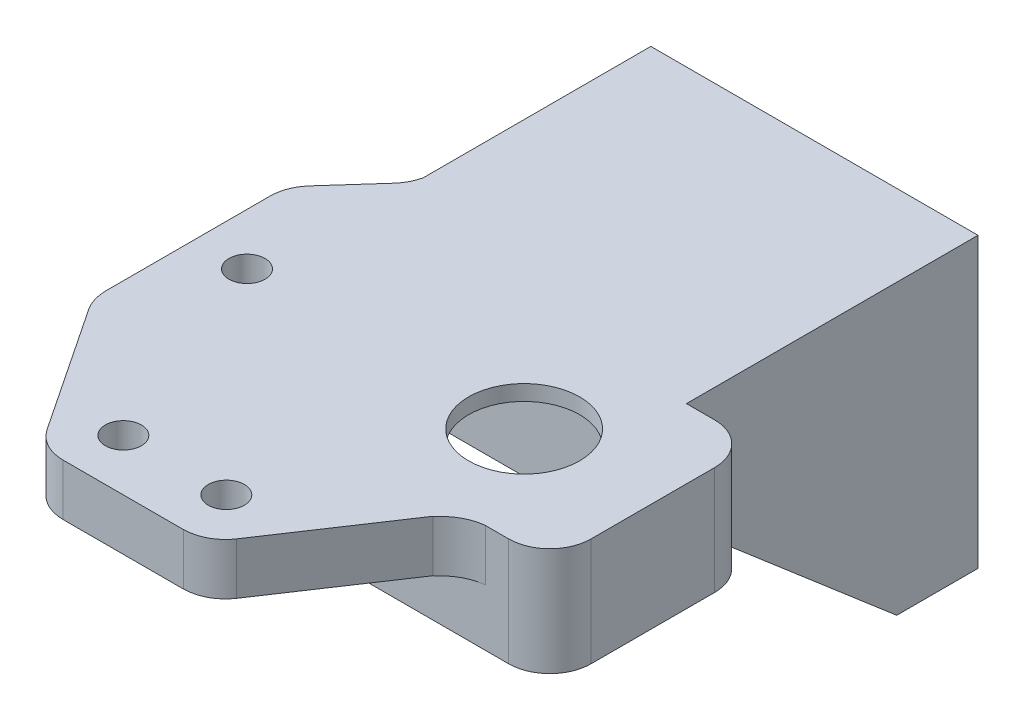
SolidWorks part; units mm, degrees
ref_plane "Alzado" through (0, 0, 0) normal (0, 0, 1) x (1, 0, 0)
ref_plane "Planta" through (0, 0, 0) normal (0, 1, 0) x (1, 0, 0)
ref_plane "Vista lateral" through (0, 0, 0) normal (1, 0, 0) x (0, 0, -1)
sketch "Croquis2" plane through (0, 0, 0) normal (0, 1, 0) x (1, 0, 0)
  line L0 (-15.9202, -3.4567) -> (19.0798, -3.4567)
  line L1 (19.0798, -3.4567) -> (19.0798, 16.5433)
  line L2 (19.0798, 16.5433) -> (-15.9202, 16.5433)
  line L3 (-15.9202, 16.5433) -> (-15.9202, -3.4567)
  dimension "D1" = 35
  dimension "D2" = 20
extrude "Saliente-Extruir1" add sketch "Croquis2" along normal blind 10.5
sketch "Croquis3" plane through (0, 0, 0) normal (0, -1, 0) x (1, 0, 0)
  line L0 (-9.9202, -0.0433) -> (-9.9202, -13.0433)
  line L1 (-9.9202, -13.0433) -> (13.0798, -13.0433)
  line L2 (13.0798, -13.0433) -> (13.0798, -0.0433)
  line L3 (13.0798, -0.0433) -> (-9.9202, -0.0433)
  line L4 (-15.9202, 3.4567) -> (19.0798, 3.4567) construction
  line L5 (19.0798, 3.4567) -> (19.0798, -16.5433) construction
  dimension "D1" = 23
  dimension "D2" = 13
  dimension "D3" = 3.5
  dimension "D4" = 6
extrude "Cortar-Extruir1" cut sketch "Croquis3" against normal blind 9
sketch "Croquis4" plane through (0, 0, 0) normal (0, -1, 0) x (1, 0, 0)
  line L0 (-9.9202, -0.0433) -> (-9.9202, -13.0433) construction
  line L1 (-15.9202, 3.4567) -> (19.0798, 3.4567) construction
  line L2 (13.0798, -13.0433) -> (13.0798, -0.0433) construction
  circle A0 centre (-12.2202, -6.5433) radius 1
  circle A1 centre (15.3798, -6.5433) radius 1
  dimension "D1" = 2
  dimension "D4" = 2.3
  dimension "D2" = 2.3
  dimension "D3" = 10
  dimension "D5" = 10
extrude "Cortar-Extruir2" cut sketch "Croquis4" against normal blind 4
sketch "Croquis5" plane through (0, 9, 0) normal (0, -1, 0) x (1, 0, 0)
  line L0 (13.0798, -0.0433) -> (-9.9202, -0.0433) construction
  line L1 (-9.9202, -0.0433) -> (-9.9202, -13.0433) construction
  circle A0 centre (6.5798, -6.5433) radius 5.386
  dimension "D1" = 10.772
  dimension "D2" = 6.5
  dimension "D3" = 16.5
extrude "Cortar-Extruir3" cut sketch "Croquis5" against normal blind 4
fillet "Redondeo1" radius 4 4 edges at (19.0798, 5.25, 3.4567) (-15.9202, 5.25, 3.4567) (-15.9202, 5.25, -16.5433) (19.0798, 5.25, -16.5433)
sketch "Croquis9" plane through (0, 10.5, 0) normal (0, 1, 0) x (1, 0, 0)
  line L0 (15.0798, 16.5433) -> (12.3366, 16.5433)
  line L1 (15.0798, 16.5433) -> (-11.9202, 16.5433) construction
  line L2 (1.8526, 25.3713) -> (9.5086, 17.7143)
  line L3 (-0.9754, 26.5433) -> (-19.3184, 26.5433)
  line L4 (-19.3184, 26.5433) -> (-19.3184, 23.5993)
  line L5 (13.0798, 0.0433) -> (-9.9202, 0.0433) construction
  line L6 (-20.3382, 20.9333) -> (-24.3012, 16.5023)
  line L7 (-25.3202, 13.8353) -> (-25.3202, -2.2447)
  line L8 (-24.6492, -4.4627) -> (-16.5092, -16.6747)
  line L9 (-13.1822, -18.4567) -> (-1.4642, -18.4567)
  line L10 (9.4928, -5.2377) -> (1.8628, -16.6747)
  line L11 (12.8208, -3.4567) -> (15.0798, -3.4567)
  line L12 (19.0798, 12.5433) -> (19.0798, 0.5433)
  arc A0 (19.0798, 12.5433) -> (15.0798, 16.5433) centre (15.0798, 12.5433) ccw construction
  arc A1 (15.0798, -3.4567) -> (19.0798, 0.5433) centre (15.0798, 0.5433) ccw construction
  spline S0 degree 2 poles (12.3366, 16.5433) (10.6986, 16.5878) (9.5086, 17.7143) knots 0 0 0 1 1 1
  spline S1 degree 2 poles (1.8526, 25.3713) (0.6624, 26.4974) (-0.9754, 26.5433) knots 0 0 0 1 1 1
  spline S2 degree 2 poles (-19.3184, 23.5993) (-19.3581, 22.0864) (-20.3382, 20.9333) knots 0 0 0 1 1 1
  spline S3 degree 2 poles (-24.3012, 16.5023) (-25.2821, 15.3489) (-25.3202, 13.8353) knots 0 0 0 1 1 1
  spline S4 degree 2 poles (-25.3202, -2.2447) (-25.2872, -3.4567) (-24.6492, -4.4627) knots 0 0 0 1 1 1
  spline S5 degree 2 poles (-16.5092, -16.6747) (-15.2925, -18.3998) (-13.1822, -18.4567) knots 0 0 0 1 1 1
  spline S6 degree 2 poles (-1.4642, -18.4567) (0.6651, -18.358) (1.8628, -16.6747) knots 0 0 0 1 1 1
  spline S7 degree 2 poles (9.4928, -5.2377) (10.9831, -3.6364) (12.8208, -3.4567) knots 0 0 0 0.396538 0.396538 0.396538
  spline S8 degree 2 poles (15.0798, -3.4567) (18.7366, -3.1135) (19.0798, 0.5433) knots 0 0 0 1 1 1
  spline S9 degree 2 poles (15.0798, 16.5433) (18.7366, 16.2002) (19.0798, 12.5433) knots 0 0 0 1 1 1
  point P5 (10.8106, 16.8583)
  point P6 (9.5086, 17.7143)
  point P9 (1.8526, 25.3713)
  point P12 (0.5506, 26.2273)
  point P13 (-0.9754, 26.5433)
  point P15 (-19.5932, 22.1763)
  point P19 (-20.3382, 20.9333)
  point P22 (-24.3012, 16.5023)
  point P25 (-25.0462, 15.2593)
  point P26 (-25.3202, 13.8353)
  point P30 (-25.0432, -3.6777)
  point P31 (-24.6492, -4.4627)
  point P33 (-16.5092, -16.6747)
  point P38 (-15.0692, -17.9827)
  point P40 (-13.1822, -18.4567)
  point P42 (0.6978, -17.8057)
  point P45 (1.8628, -16.6747)
  point P47 (9.4928, -5.2377)
  point P50 (12.8208, -3.4567)
  point P58 (17.9082, 15.3717)
  point P59 (17.9082, -2.2851)
  dimension "D1" = 2.7431
  dimension "D2" = 1.526
  dimension "D3" = 3.815
  dimension "D4" = 1.302
  dimension "D5" = 4.671
  dimension "D6" = 7.656
  dimension "D7" = 12.328
  dimension "D8" = 1.302
  dimension "D9" = 13.184
  dimension "D10" = 1.526
  dimension "D11" = 13.5
  dimension "D12" = 18.343
  dimension "D13" = 2.944
  dimension "D14" = 4.367
  dimension "D15" = 9.673
  dimension "D16" = 5.61
  dimension "D17" = 10.418
  dimension "D18" = 10.041
  dimension "D19" = 14.381
  dimension "D20" = 11.284
  dimension "D21" = 15.126
  dimension "D22" = 15.4
  dimension "D23" = 12.708
  dimension "D24" = 16.08
  dimension "D25" = 0.277
  dimension "D26" = 0.394
  dimension "D27" = 1.433
  dimension "D28" = 0.785
  dimension "D29" = 8.14
  dimension "D30" = 16.718
  dimension "D31" = 1.44
  dimension "D32" = 18.026
  dimension "D33" = 1.887
  dimension "D34" = 18.5
  dimension "D35" = 11.718
  dimension "D36" = 2.162
  dimension "D37" = 17.849
  dimension "D38" = 1.165
  dimension "D39" = 16.718
  dimension "D40" = 5.281
  dimension "D41" = 3.587
  dimension "D42" = 3.328
  dimension "D43" = 3.5
  dimension "D44" = 2.259
extrude "Saliente-Extruir2" add sketch "Croquis9" against normal blind 5
sketch "Croquis13" plane through (0, 0, 0) normal (0, -1, 0) x (1, 0, 0)
  line L0 (-9.9202, -0.0433) -> (-9.9202, -13.0433)
  line L1 (-9.9202, -13.0433) -> (13.0798, -13.0433)
  line L2 (13.0798, -13.0433) -> (13.0798, -0.0433)
  line L3 (13.0798, -0.0433) -> (-9.9202, -0.0433)
extrude "Cortar-Extruir4" cut sketch "Croquis13" against normal blind 9
sketch "Croquis14" plane through (0, 9, 0) normal (0, -1, 0) x (1, 0, 0)
  line L0 (13.0798, -0.0433) -> (-9.9202, -0.0433) construction
  line L1 (-9.9202, -0.0433) -> (-9.9202, -13.0433) construction
  circle A0 centre (6.5798, -6.5433) radius 5.386
  dimension "D3" = 10.772
  dimension "D1" = 6.5
  dimension "D2" = 16.5
extrude "Cortar-Extruir5" cut sketch "Croquis14" against normal up to next
sketch "Croquis15" plane through (0, 10.5, 0) normal (0, 1, 0) x (1, 0, 0)
  line L0 (-9.9202, 0.0433) -> (-9.9202, 13.0433) construction
  line L1 (13.0798, 0.0433) -> (-9.9202, 0.0433) construction
  line L2 (-24.6492, -4.4627) -> (-16.5092, -16.6747) construction
  line L3 (1.8628, -16.6747) -> (9.4928, -5.2377) construction
  circle A0 centre (-20.3202, 6.5443) radius 1.75
  circle A1 centre (-12.3243, -13.4532) radius 1.75
  circle A2 centre (-2.3243, -13.4567) radius 1.75
  dimension "D1" = 3.5
  dimension "D4" = 3.5
  dimension "D2" = 10.4
  dimension "D3" = 7.291
  dimension "D5" = 10
  dimension "D6" = 13.5
  dimension "D7" = 5.269
  dimension "D8" = 5.269
extrude "Cortar-Extruir6" cut sketch "Croquis15" against normal up to next
sketch "Croquis16" plane through (0, 10.5, 0) normal (0, 1, 0) x (1, 0, 0)
  line L0 (-19.3184, 26.5433) -> (-19.3184, 44.8418)
  line L1 (-19.3184, 44.8418) -> (12.3366, 44.8418)
  line L2 (12.3366, 16.5433) -> (12.3366, 44.8418)
  line L3 (-19.3184, 26.5433) -> (-0.9754, 26.5433)
  line L4 (1.8526, 25.3713) -> (9.5086, 17.7143)
  parabola Q0 (12.3366, 16.5433) -> (9.5086, 17.7143) focus (11.5758, 18.7062) apex (10.8106, 16.8583) construction
  parabola Q1 (1.8526, 25.3713) -> (-0.9754, 26.5433) focus (-0.2166, 24.3763) apex (0.5506, 26.2273) construction
  spline S0 degree 2 poles (9.5086, 17.7143) (10.6986, 16.5878) (12.3366, 16.5433) knots 0 0 0 1 1 1
  spline S1 degree 2 poles (-0.9754, 26.5433) (0.6624, 26.4974) (1.8526, 25.3713) knots 0 0 0 1 1 1
sketch "Croquis17" plane through (19.0798, 0, 0) normal (1, 0, 0) x (0, 0, -1)
  line L0 (44.8418, 10.5) -> (44.8418, -17.5)
  line L1 (16.5433, 10.5) -> (44.8418, 10.5) construction
  line L2 (44.8418, -17.5) -> (16.5433, -17.5)
  line L3 (16.5433, -17.5) -> (16.5433, 10.5)
  line L4 (16.5433, 10.5) -> (44.8418, 10.5)
  dimension "D1" = 28
extrude "Saliente-Extruir5" add sketch "Croquis17" against normal blind 38.5
sketch "Croquis18" plane through (0, 10.5, 0) normal (0, 1, 0) x (1, 0, 0)
  line L0 (12.3366, 16.5433) -> (19.0798, 16.5433)
  line L1 (19.0798, 16.5433) -> (19.0798, 44.8418)
  line L2 (19.0798, 44.8418) -> (12.3366, 44.8418)
  line L3 (12.3366, 44.8418) -> (12.3366, 16.5433)
extrude "Cortar-Extruir7" cut sketch "Croquis18" against normal blind 38.5
sketch "Croquis19" plane through (0, 0, -16.5433) normal (0, 0, 1) x (1, 0, 0)
  line L0 (-16.4202, -17.5) -> (9.3366, -17.5)
  line L1 (-19.4202, -17.5) -> (12.3366, -17.5) construction
  line L2 (9.3366, -17.5) -> (9.3366, 2.5)
  line L3 (9.3366, 2.5) -> (-16.4202, 2.5)
  line L4 (-16.4202, 2.5) -> (-16.4202, -17.5)
  line L5 (-19.4202, 5.5) -> (-19.4202, -17.5) construction
  line L6 (12.3366, -17.5) -> (12.3366, 0) construction
  line L7 (-19.4202, 5.5) -> (-11.9202, 5.5) construction
  dimension "D1" = 3
  dimension "D2" = 3
  dimension "D3" = 3
extrude "Cortar-Extruir8" cut sketch "Croquis19" against normal blind 20.5
sketch "Croquis20" plane through (0, 0, -37.0433) normal (0, 0, 1) x (1, 0, 0)
  line L0 (-16.4202, -17.5) -> (9.3366, -17.5) construction
  line L1 (-13.1822, 5.5) -> (-1.4642, 5.5) construction
  line L2 (-19.4202, 5.5) -> (-19.4202, -17.5) construction
  line L3 (-7.0418, -2.5) -> (-0.0418, -2.5)
  line L5 (-0.0418, -9.5) -> (-7.0418, -9.5)
  arc A0 (-7.0418, -2.5) -> (-7.0418, -9.5) centre (-7.0418, -6) ccw
  arc A1 (-0.0418, -2.5) -> (-0.0418, -9.5) centre (-0.0418, -6) cw
  point P0 (-3.5418, -17.5)
  point P1 (-3.5418, 5.5)
  point P4 (-19.4202, -6)
  point P7 (-3.5418, -6)
  dimension "D1" = 7
  dimension "D2" = 7
  dimension "D3" = 3.5
extrude "Cortar-Extruir9" cut sketch "Croquis20" against normal blind 3
sketch "Croquis21" plane through (0, 0, -40.0433) normal (0, 0, 1) x (1, 0, 0)
  circle A0 centre (-3.5418, -6) radius 2.49
  circle A3 centre (-8.0418, -6) radius 1.3
  circle A4 centre (0.9582, -6) radius 1.3
  dimension "D1" = 4.98
  dimension "D2" = 2.6
  dimension "D3" = 2.6
  dimension "D4" = 4.5
  dimension "D5" = 4.5
extrude "Cortar-Extruir10" cut sketch "Croquis21" against normal blind 5
sketch "Croquis22" plane through (12.3366, 0, 0) normal (1, 0, 0) x (0, 0, -1)
  line L1 (16.5433, -17.5) -> (44.8418, -17.5) construction
  line L2 (16.5433, 0) -> (36.9544, -17.5)
  line L3 (16.5433, 0) -> (16.5433, -17.5)
  line L4 (16.5433, -17.5) -> (36.9544, -17.5)
extrude "Cortar-Extruir11" cut sketch "Croquis22" against normal blind 32
